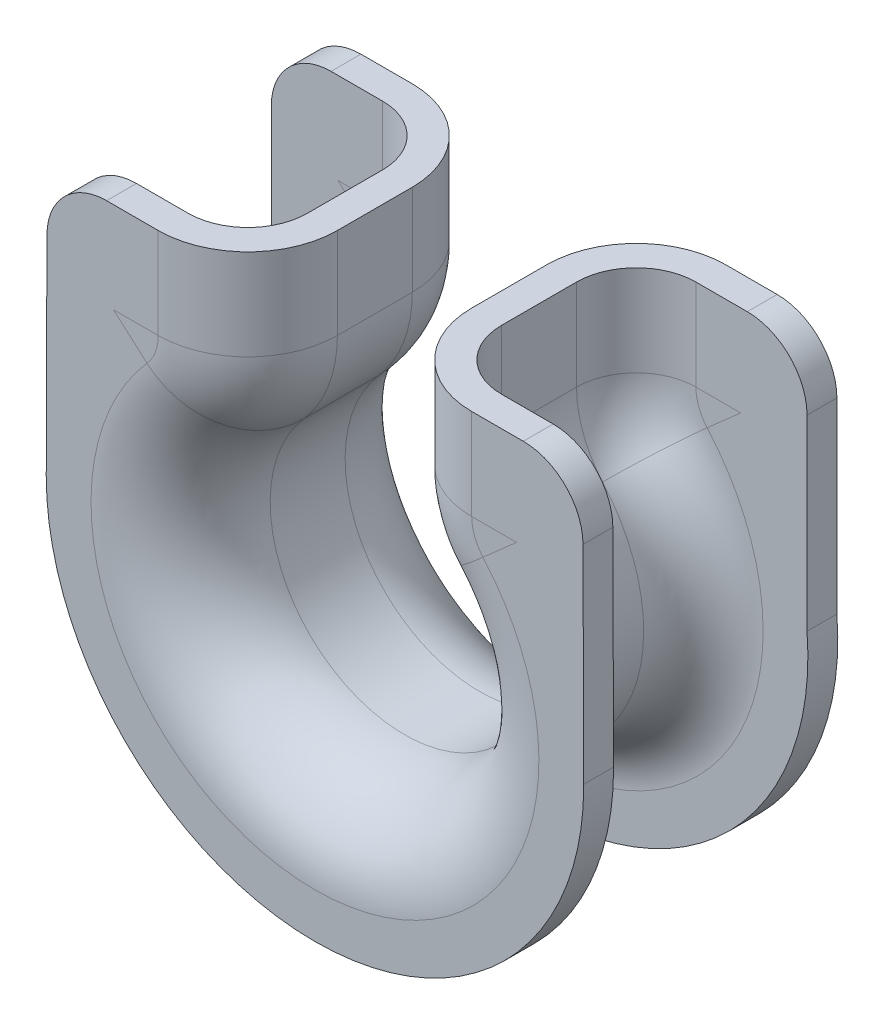
SolidWorks part; units mm, degrees
material "Polyetheretherketone (PEEK)"
ref_plane "Front Plane" through (0, 0, 0) normal (0, 0, 1) x (1, 0, 0)
ref_plane "Top Plane" through (0, 0, 0) normal (0, 1, 0) x (1, 0, 0)
ref_plane "Right Plane" through (0, 0, 0) normal (1, 0, 0) x (0, 0, -1)
sketch "Sketch2" plane through (0, 0, 0) normal (0, 0, 1) x (1, 0, 0)
  line L0 (-4.5, 11.9059) -> (-4.5, 18)
  line L1 (0, -3.213) -> (0, 3.213) construction
  line L2 (4.5, 11.9059) -> (4.5, 18)
  line L3 (0, -9) -> (0, -5.3794) construction
  arc A0 (6.75, 5.9529) -> (-6.75, 5.9529) centre (0, 0) cw
  arc A1 (-6.75, 5.9529) -> (-4.5, 11.9059) centre (-13.5, 11.9059) ccw
  arc A2 (6.75, 5.9529) -> (4.5, 11.9059) centre (13.5, 11.9059) cw
  dimension "D1" = 9
  dimension "D2" = 9
  dimension "D3" = 18
  dimension "D4" = 9
sketch "Sketch5" plane through (0, 0, 0) normal (1, 0, 0) x (0, 0, -1)
  line L0 (-2.509, -9) -> (2.509, -9)
  line L2 (0, 9.9) -> (0, -9.9) construction
  line L3 (-8.509, -15) -> (-8.509, -18)
  line L4 (8.509, -15) -> (8.509, -18)
  line L5 (6.509, -15) -> (6.509, -18)
  line L6 (-2.509, -11) -> (2.509, -11)
  line L7 (-6.509, -15) -> (-6.509, -18)
  line L8 (-8.509, -18) -> (-6.509, -18)
  line L9 (6.509, -18) -> (8.509, -18)
  arc A0 (-2.509, -9) -> (-8.509, -15) centre (-2.509, -15) ccw
  arc A1 (2.509, -9) -> (8.509, -15) centre (2.509, -15) cw
  arc A2 (2.509, -11) -> (6.509, -15) centre (2.509, -15) cw
  arc A3 (-2.509, -11) -> (-6.509, -15) centre (-2.509, -15) ccw
  point P4 (0, -9)
  dimension "D1" = 6
  dimension "D2" = 3
  dimension "D3" = 2
sweep "Sweep2" add profiles "Sketch5" path "Sketch2"
sketch "Sketch7" plane through (0, 0, 0) normal (0, 0, 1) x (1, 0, 0)
  line L0 (17.9407, -1.4599) -> (17.9407, 18)
  line L1 (17.9407, 18) -> (13.5, 18)
  line L2 (13.5, 18) -> (13.5, 11.9059)
  line L3 (0, -9.3599) -> (0, 9.3599) construction
  line L4 (-13.5, 18) -> (-13.5, 11.9059)
  line L5 (-17.9407, 18) -> (-13.5, 18)
  line L6 (-17.9407, -1.4599) -> (-17.9407, 18)
  arc A0 (-13.5, 11.9059) -> (13.5, 11.9059) centre (0, 0) ccw construction
  arc A1 (13.5, 11.9059) -> (17.9407, -1.4599) centre (-4.3941, -1.4599) cw
  arc A2 (-13.5, 11.9059) -> (-17.9407, -1.4599) centre (4.3941, -1.4599) ccw
extrude "Boss-Extrude1" add sketch "Sketch7" along normal blind 2 from surface at -8.509 starting at face at (-12, 14.9529, -8.509)
sketch "Sketch9" plane through (0, 0, 0) normal (0, 0, 1) x (1, 0, 0)
  line L0 (18, 0) -> (17.9407, 18)
  line L1 (17.9407, 18) -> (13.5, 18)
  line L2 (13.5, 18) -> (13.5, 11.9059)
  line L3 (0, -9.3599) -> (0, 9.3599) construction
  line L4 (-13.5, 18) -> (-13.5, 11.9059)
  line L5 (-17.9407, 18) -> (-13.5, 18)
  line L6 (-18, 0) -> (-17.9407, 18)
  arc A0 (-13.5, 11.9059) -> (13.5, 11.9059) centre (0, 0) ccw construction
  arc A1 (13.5, 11.9059) -> (18, 0) centre (-0.1583, -0.0598) cw
  arc A2 (-13.5, 11.9059) -> (-18, 0) centre (0.1583, -0.0598) ccw
extrude "Boss-Extrude2" add sketch "Sketch9" against normal blind 2 from surface at 8.509 starting at face at (-12, 14.9529, 8.509)
fillet "Fillet1" radius 4 4 edges at (17.9407, 18, 7.509) (17.9407, 18, -7.509) (-17.9407, 18, 7.509) (-17.9407, 18, -7.509)
